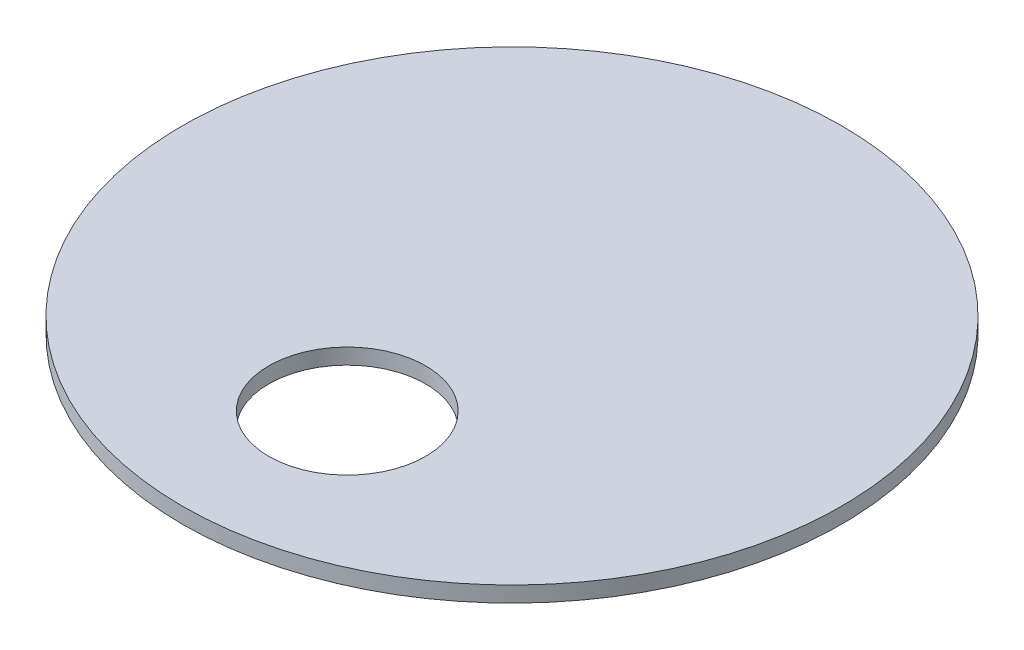
SolidWorks part; units mm, degrees
ref_plane "Front Plane" through (0, 0, 0) normal (0, 0, 1) x (1, 0, 0)
ref_plane "Top Plane" through (0, 0, 0) normal (0, 1, 0) x (1, 0, 0)
ref_plane "Right Plane" through (0, 0, 0) normal (1, 0, 0) x (0, 0, -1)
sketch "Sketch1" plane through (0, 0, 0) normal (0, 1, 0) x (1, 0, 0)
  line L0 (0, 0) -> (0, -105) construction
  circle A0 centre (0, 0) radius 105
  circle A1 centre (0, -52.5) radius 25
  point P5 (0, -52.5)
  dimension "D1" = 50
  dimension "D2" = 210
extrude "Boss-Extrude4" add sketch "Sketch1" along normal blind 5
